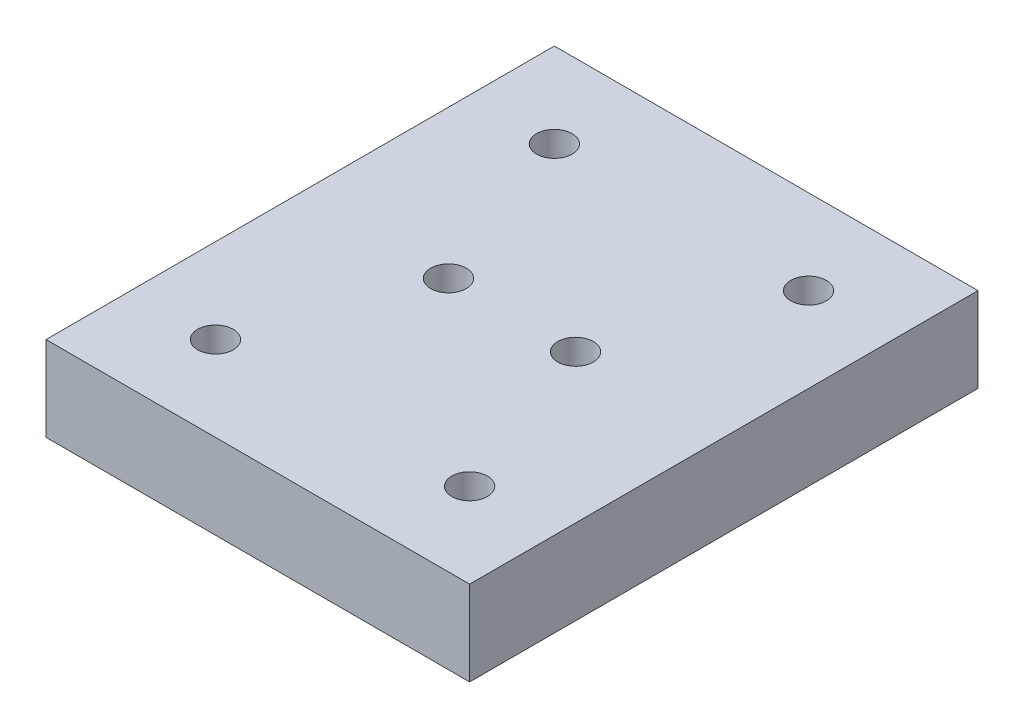
SolidWorks part; units mm, degrees
ref_plane "Front Plane" through (0, 0, 0) normal (0, 0, 1) x (1, 0, 0)
ref_plane "Top Plane" through (0, 0, 0) normal (0, 1, 0) x (1, 0, 0)
ref_plane "Right Plane" through (0, 0, 0) normal (1, 0, 0) x (0, 0, -1)
sketch "Sketch1" plane through (0, 0, 0) normal (0, 1, 0) x (1, 0, 0)
  line L1 (-25, -30) -> (25, -30)
  line L2 (-25, -30) -> (-25, 30)
  line L3 (-25, 30) -> (25, 30)
  line L4 (25, -30) -> (25, 30)
  line L5 (-25, -30) -> (25, 30) construction
  line L6 (-25, 30) -> (25, -30) construction
  point P0 (0, 0)
  dimension "D1" = 50
  dimension "D2" = 60
extrude "Boss-Extrude1" add sketch "Sketch1" along normal blind 10
hole_wizard "M5 Tapped Hole1" positions "Sketch4" profile "Sketch3" tap size "M5" standard "ISO" end condition through all
sketch "Sketch4" plane through (0, 10, 0) normal (0, 1, 0) x (1, 0, 0)
  point P0 (-7.5, 0)
  point P2 (7.5, 0)
  dimension "D1" = 15
  dimension "D2" = 7.5
sketch "Sketch3" plane through (-7.5, 10, 0) normal (1, 0, 0) x (0, 0, 1)
  line L0 (0, 0) -> (0, 10)
  line L1 (0, 10) -> (2.1, 10)
  line L2 (2.1, 10) -> (2.1, 0)
  line L5 (2.1, 0) -> (0, 0)
  line L11 (0, -6.35) -> (0, 107.95) construction
  dimension "Thru Tap Drill Dia." = 4.2
  dimension "Thru Tap Drill Depth" = 10
cosmetic thread "Hole Thread1" parameters "D2"=5
cosmetic thread "Hole Thread2" parameters "D2"=5
hole_wizard "M5 Tapped Hole2" positions "Sketch6" profile "Sketch5" tap size "M5" standard "ISO" end condition through all
sketch "Sketch6" plane through (0, 10, 0) normal (0, 1, 0) x (1, 0, 0)
  line L0 (25, -30) -> (25, 30) construction
  line L1 (-25, 30) -> (-25, -30) construction
  line L2 (25, 30) -> (-25, 30) construction
  line L3 (-25, -30) -> (25, -30) construction
  point P0 (15, 20)
  point P2 (-15, 20)
  point P4 (-15, -20)
  point P6 (15, -20)
  dimension "D1" = 10
  dimension "D2" = 10
  dimension "D3" = 10
  dimension "D4" = 10
  dimension "D5" = 10
  dimension "D6" = 10
  dimension "D7" = 10
  dimension "D8" = 10
sketch "Sketch5" plane through (15, 10, -20) normal (1, 0, 0) x (0, 0, 1)
  line L0 (0, 0) -> (0, 10)
  line L1 (0, 10) -> (2.1, 10)
  line L2 (2.1, 10) -> (2.1, 0)
  line L5 (2.1, 0) -> (0, 0)
  line L11 (0, -6.35) -> (0, 107.95) construction
  dimension "Thru Tap Drill Dia." = 4.2
  dimension "Thru Tap Drill Depth" = 10
cosmetic thread "Hole Thread3"
cosmetic thread "Hole Thread4"
cosmetic thread "Hole Thread5"
cosmetic thread "Hole Thread6"
